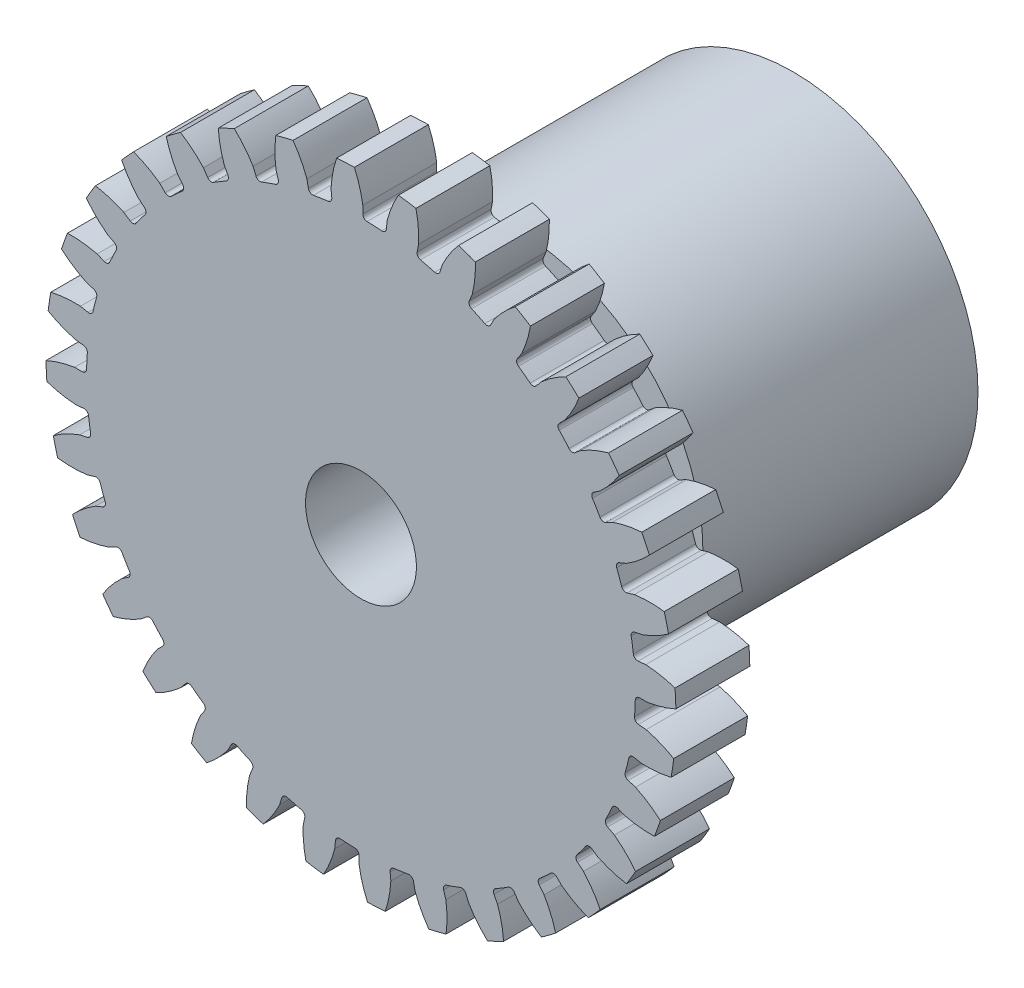
SolidWorks part; units mm, degrees
ref_plane "Front" through (0, 0, 0) normal (0, 0, 1) x (1, 0, 0)
ref_plane "Top" through (0, 0, 0) normal (0, 1, 0) x (1, 0, 0)
ref_plane "Right" through (0, 0, 0) normal (1, 0, 0) x (0, 0, -1)
sketch "Sketch1" plane through (0, 0, 0) normal (0, 0, 1) x (1, 0, 0)
  line L0 (-406.4, 0) -> (406.4, 0) construction
  circle A0 centre (0, 0) radius 27.051
  circle A1 centre (0, 0) radius 25.4 construction
  circle A3 centre (0, 0) radius 23.5633 construction
  dimension "D1" = 1.8367
  dimension "D2" = 3.4877
  dimension "D3" = 1.651
extrude "Boss-Extrude1" add sketch "Sketch1" against normal blind 6.35
sketch "Sketch2" plane through (0, 0, 0) normal (1, 0, 0) x (0, 0, -1)
  line L0 (6.35, 0) -> (25.4, 0)
  line L1 (6.35, 0) -> (6.35, 22.225)
  line L2 (6.35, 22.225) -> (25.4, 22.225)
  line L3 (25.4, 22.225) -> (25.4, 0)
  point P5 (25.4, -22.225)
  point P6 (0, -27.051)
  point P7 (6.35, -27.051)
  point P9 (0, 27.051)
sketch "Sketch3" plane through (0, 0, 0) normal (0, 0, 1) x (1, 0, 0)
  line L0 (0, 0) -> (0, 27.051) construction
  line L1 (-6.1571, 23.8077) -> (0, 25.4)
  line L2 (-9.5921, 25.4) -> (9.5921, 25.4) construction
  line L3 (-9.2865, 22.9983) -> (9.2865, 27.8017) construction
  line L4 (-6.1571, 23.8077) -> (0, 0) construction
  line L5 (-15.7046, 18.923) -> (0, 0) construction
  line L6 (-15.7046, 18.923) -> (-2.4913, 29.889) construction
  line L7 (-4.2933, 24.2133) -> (0, 0) construction
  line L8 (-4.2933, 24.2133) -> (0.0901, 24.9905) construction
  arc A0 (-6.1571, 23.8077) -> (-15.7046, 18.923) centre (0, 0) ccw
  circle A1 centre (0, 0) radius 25.4 construction
  circle A2 centre (0, 0) radius 24.591 construction
  arc A3 (-6.1571, 23.8077) -> (-4.2933, 24.2133) centre (0, 0) cw
  circle A4 centre (0, 0) radius 27.051 construction
  point P6 (0, 25.4)
  dimension "D1" = 6.3597
  dimension "Pressure Angle" = 14.5
  dimension "D2" = 10.8114
  dimension "D3" = 17.1711
  dimension "D4" = 1.9079
  dimension "D5" = 4.4518
sketch "Sketch4" plane through (0, 0, 0) normal (0, 0, 1) x (1, 0, 0)
  line L0 (0, 0) -> (1.2448, 25.3388) construction
  line L1 (0.1603, 24.5904) -> (0.1603, 23.5627)
  line L2 (0, 25.4) -> (2.4896, 25.2777) construction
  line L3 (2.2508, 24.4877) -> (2.1501, 23.465)
  line L4 (0.1603, 23.5627) -> (0, 0) construction
  line L5 (0, 0) -> (0, 27.051) construction
  line L6 (-15.7046, 18.923) -> (-2.4913, 29.889) construction
  line L7 (-15.7046, 18.923) -> (-2.4913, 29.889) construction
  arc A0 (2.1501, 23.465) -> (0.1603, 23.5627) centre (0, 0) ccw
  arc A1 (0, 25.4) -> (2.4896, 25.2777) centre (0, 0) cw construction
  circle A2 centre (0, 0) radius 25.4 construction
  circle A3 centre (0, 0) radius 24.591 construction
  circle A4 centre (0, 0) radius 23.5633 construction
  arc A5 (5.409, 29.5009) -> (-2.4913, 29.889) centre (0, 0) ccw
  spline S0 degree 2 poles (-2.4913, 29.889) (-0.2935, 27.5377) (0.1603, 24.5904) knots 0 0 0 1 1 1
  spline S1 degree 2 poles (5.409, 29.5009) (2.9913, 27.3764) (2.2508, 24.4877) knots 0 0 0 1 1 1
  dimension "D1" = 2.4936
extrude "Cut-Extrude1" cut sketch "Sketch4" against normal through all
fillet "Fillet1" radius 0.374 2 edges at (2.1501, 23.465, -3.175) (0.1603, 23.5627, -3.175)
pattern_circular "CirPattern1" count 32 over 360 about axis through (0, 0, -6.35) along (0, 0, 1) of "Cut-Extrude1", "Fillet1"
sketch "Pitch Dia" plane through (0, 0, 0) normal (0, 0, 1) x (1, 0, 0)
  circle A0 centre (0, 0) radius 25.4 construction
  circle A1 centre (0, 0) radius 25.4
sketch "Sketch5" plane through (0, 0, -6.35) normal (0, 0, -1) x (-1, 0, 0)
  circle A0 centre (0, 0) radius 11.1125
  dimension "D1" = 22.225
extrude "Boss-Extrude2" add sketch "Sketch5" along normal blind 7.1437
sketch "Sketch6" plane through (0, 0, -13.4937) normal (0, 0, -1) x (-1, 0, 0)
  circle A0 centre (0, 0) radius 15.875
  dimension "D1" = 31.75
extrude "Boss-Extrude3" add sketch "Sketch6" along normal blind 23.622
sketch "Sketch7" plane through (0, 0, -37.1157) normal (0, 0, -1) x (-1, 0, 0)
  circle A0 centre (0, 0) radius 4.7625
  dimension "D1" = 9.525
extrude "Cut-Extrude2" cut sketch "Sketch7" against normal through all
equation "\"D1@Boss-Extrude1\" = \"Face Wd@Sketch2\""
equation "\"D1@Sketch4\" = 1.5708/(\"Number of Teeth@Sketch1\"/\"Ptich Dia@Sketch1\")"
equation "\"D1@CirPattern1\" = \"Number of Teeth@Sketch1\""
equation "\"D1@Fillet1\" = \"D1@Sketch4\"*.15"
